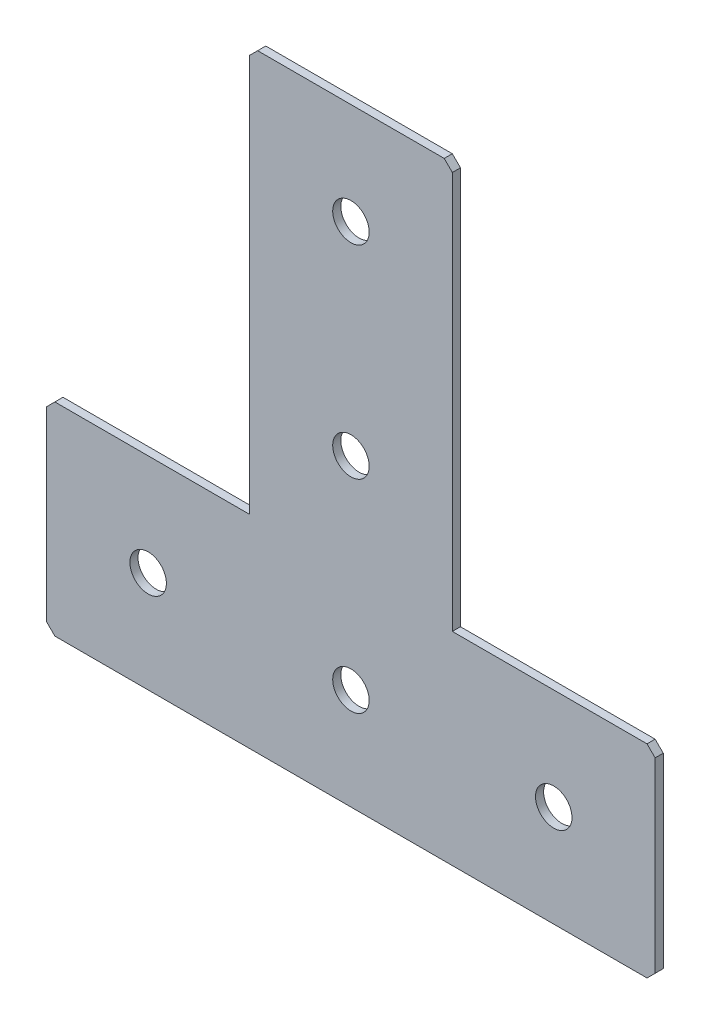
SolidWorks part; units mm, degrees
material "Простая углеродистая сталь"
ref_plane "Спереди(Плоскость XY)" through (0, 0, 0) normal (0, 0, 1) x (1, 0, 0)
ref_plane "Сверху(Плоскость XZ)" through (0, 0, 0) normal (0, 1, 0) x (1, 0, 0)
ref_plane "Справа(Плоскость ZY)" through (0, 0, 0) normal (1, 0, 0) x (0, 0, -1)
sketch "Эскиз1" plane through (0, 0, 0) normal (0, 0, -1) x (1, 0, 0)
  line L0 (0, 0) -> (0, 150) construction
  line L1 (-75, 150) -> (75, 150)
  line L2 (75, 150) -> (75, 100)
  line L3 (75, 100) -> (25, 100)
  line L4 (25, 100) -> (25, 0)
  line L5 (25, 0) -> (-25, 0)
  line L6 (-75, 150) -> (-75, 100)
  line L7 (-75, 100) -> (-25, 100)
  line L8 (-25, 100) -> (-25, 0)
  line L10 (-75, 125) -> (75, 125) construction
  dimension "D1" = 150
  dimension "D3" = 50
extrude "Бобышка-Вытянуть1" add sketch "Эскиз1" along normal blind 2
hole_wizard "Отверстие с зазором M81" positions "Эскиз2" profile "Эскиз3" hole size "M8" standard "DIN" end condition through all
sketch "Эскиз2" plane through (0, 0, -2) normal (0, 0, -1) x (1, 0, 0)
  line L6 (0, 0) -> (0, 150) construction
  line L7 (75, 150) -> (-75, 150) construction
  line L9 (-75, 125) -> (75, 125) construction
  line L10 (-75, 150) -> (-75, 100) construction
  line L11 (75, 100) -> (75, 150) construction
  point P38 (0, 125)
  point P40 (-50, 125)
  point P42 (50, 125)
  point P44 (0, 75)
  point P46 (0, 25)
  dimension "D1" = 50
  dimension "D2" = 50
  dimension "D3" = 50
  dimension "D4" = 50
sketch "Эскиз3" plane through (0, -25, -2) normal (1, 0, 0) x (0, 1, 0)
  line L0 (0, 0) -> (0, 2)
  line L1 (0, 2) -> (4.5, 2)
  line L2 (4.5, 2) -> (4.5, 0)
  line L5 (4.5, 0) -> (0, 0)
  line L11 (0, -6.35) -> (0, 107.95) construction
  dimension "Диаметр сквозного отверстия" = 9
  dimension "Глубина сквозного отверстия" = 2
chamfer "Фаска1" distance 2 angle 45 6 edges at (25, 0, -1) (75, -100, -1) (75, -150, -1) (-75, -150, -1) (-75, -100, -1) (-25, 0, -1)
